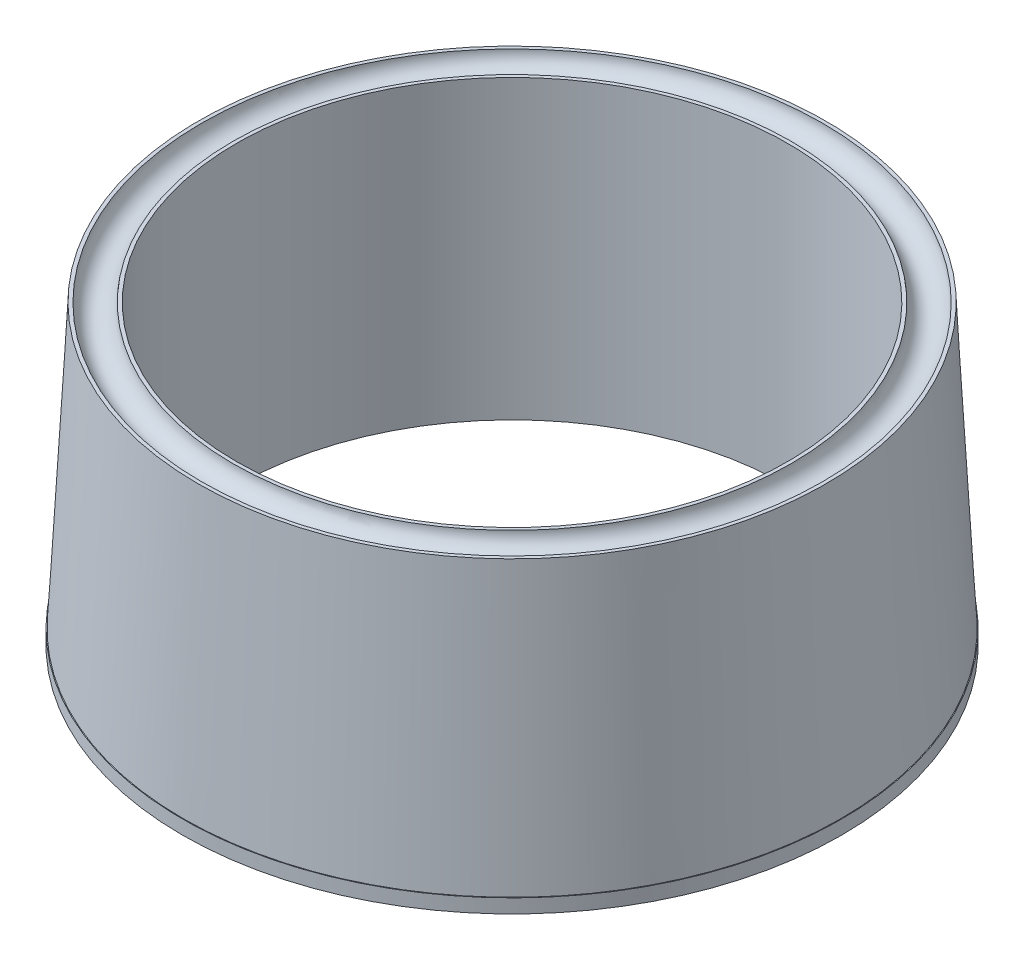
SolidWorks part; units mm, degrees
ref_plane "Płaszczyzna przednia" through (0, 0, 0) normal (0, 0, 1) x (1, 0, 0)
ref_plane "Płaszczyzna górna" through (0, 0, 0) normal (0, 1, 0) x (1, 0, 0)
ref_plane "Płaszczyzna prawa" through (0, 0, 0) normal (1, 0, 0) x (0, 0, -1)
sketch "Sketch1" plane through (0, 0, 0) normal (0, 1, 0) x (1, 0, 0)
  circle A0 centre (0, 0) radius 45
extrude "Boss-Extrude1" add sketch "Sketch1" along normal blind 42.5
sketch "Sketch2" plane through (0, 42.5, 0) normal (0, 1, 0) x (1, 0, 0)
  circle A0 centre (0, 0) radius 39.5
extrude "Cut-Extrude1" cut sketch "Sketch2" against normal blind 148
draft "Draft2" type of draft neutral plane draft angle 3 faces to draft 1 face at (0, 42.5, 45) neutral plane through (0, 42.5, 0) neutral plane normal (0, 1, 0) parameters "D1"=3
sketch "Sketch5" plane through (0, 0, 0) normal (0, -1, 0) x (1, 0, 0)
  line L0 (-39.5, 0) -> (-47.2273, 0)
  circle A0 centre (0, 0) radius 39.5 construction
  circle A1 centre (0, 0) radius 47.2273 construction
  dimension "D1" = 7.7273
sketch "Sketch6" plane through (0, 0, 0) normal (0, -1, 0) x (1, 0, 0)
  line L0 (-39.5, 0) -> (-47.2273, 0) construction
  line L1 (-43.3637, 0) -> (-21.6818, -37.554)
  line L2 (-21.6818, -37.554) -> (21.6818, -37.554)
  line L3 (21.6818, -37.554) -> (43.3637, 0)
  line L4 (43.3637, 0) -> (21.6818, 37.554)
  line L5 (21.6818, 37.554) -> (-21.6818, 37.554)
  line L6 (-21.6818, 37.554) -> (-43.3637, 0)
  line L7 (-21.6818, 34.2054) -> (-18.7818, 35.8797)
  line L8 (-18.7818, 35.8797) -> (-18.7818, 39.2284)
  line L9 (-18.7818, 39.2284) -> (-21.6818, 40.9027)
  line L10 (-21.6818, 40.9027) -> (-24.5818, 39.2284)
  line L11 (-24.5818, 39.2284) -> (-24.5818, 35.8797)
  line L12 (-24.5818, 35.8797) -> (-21.6818, 34.2054)
  line L13 (21.6818, 34.2054) -> (24.5818, 35.8797)
  line L14 (24.5818, 35.8797) -> (24.5818, 39.2284)
  line L15 (24.5818, 39.2284) -> (21.6818, 40.9027)
  line L16 (21.6818, 40.9027) -> (18.7818, 39.2284)
  line L17 (18.7818, 39.2284) -> (18.7818, 35.8797)
  line L18 (18.7818, 35.8797) -> (21.6818, 34.2054)
  line L19 (43.3637, -3.3486) -> (46.2637, -1.6743)
  line L20 (46.2637, -1.6743) -> (46.2637, 1.6743)
  line L21 (46.2637, 1.6743) -> (43.3637, 3.3486)
  line L22 (43.3637, 3.3486) -> (40.4637, 1.6743)
  line L23 (40.4637, 1.6743) -> (40.4637, -1.6743)
  line L24 (40.4637, -1.6743) -> (43.3637, -3.3486)
  line L25 (-43.3637, -3.3486) -> (-40.4637, -1.6743)
  line L26 (-40.4637, -1.6743) -> (-40.4637, 1.6743)
  line L27 (-40.4637, 1.6743) -> (-43.3637, 3.3486)
  line L28 (-43.3637, 3.3486) -> (-46.2637, 1.6743)
  line L29 (-46.2637, 1.6743) -> (-46.2637, -1.6743)
  line L30 (-46.2637, -1.6743) -> (-43.3637, -3.3486)
  line L31 (-21.6818, -34.2054) -> (-24.5818, -35.8797)
  line L32 (-24.5818, -35.8797) -> (-24.5818, -39.2284)
  line L33 (-24.5818, -39.2284) -> (-21.6818, -40.9027)
  line L34 (-21.6818, -40.9027) -> (-18.7818, -39.2284)
  line L35 (-18.7818, -39.2284) -> (-18.7818, -35.8797)
  line L36 (-18.7818, -35.8797) -> (-21.6818, -34.2054)
  line L37 (21.6818, -40.9027) -> (24.5818, -39.2284)
  line L38 (24.5818, -39.2284) -> (24.5818, -35.8797)
  line L39 (24.5818, -35.8797) -> (21.6818, -34.2054)
  line L40 (21.6818, -34.2054) -> (18.7818, -35.8797)
  line L41 (18.7818, -35.8797) -> (18.7818, -39.2284)
  line L42 (18.7818, -39.2284) -> (21.6818, -40.9027)
  circle A0 centre (0, 0) radius 37.554 construction
  circle A1 centre (-21.6818, 37.554) radius 2.9 construction
  circle A2 centre (21.6818, 37.554) radius 2.9 construction
  circle A3 centre (43.3637, 0) radius 2.9 construction
  circle A4 centre (-43.3637, 0) radius 2.9 construction
  circle A5 centre (-21.6818, -37.554) radius 2.9 construction
  circle A6 centre (21.6818, -37.554) radius 2.9 construction
  dimension "D1" = 2.9
  dimension "D2" = 0.9637
  dimension "D3" = 2.9
  dimension "D4" = 2.9
  dimension "D5" = 2.9
  dimension "D6" = 2.9
  dimension "D7" = 2.9
  dimension "D8" = 2.9
  dimension "D9" = 43.3637
extrude "Cut-Extrude2" cut sketch "Sketch6" against normal blind 5 contours L11 L12 L6 L5 L8 L9 L10 | L16 L17 L5 L4 L13 L14 L15 | L3 L24 L19 L20 L21 L22 L4 | L41 L42 L37 L38 L39 L3 L2 | L34 L35 L2 L1 L31 L32 L33 | L29 L30 L25 L1 L6 L27 L28 | L26 L27 L6 L1 L25 | L6 L12 L7 L8 L5 | L17 L18 L13 L4 L5 | L23 L24 L3 L4 L22 | L40 L41 L2 L3 L39 | L35 L36 L31 L1 L2
sketch "Sketch7" plane through (0, 0, 0) normal (0, -1, 0) x (1, 0, 0)
  circle A0 centre (0, 0) radius 47.2273
extrude "Boss-Extrude2" add sketch "Sketch7" against normal blind 2
sketch "Sketch8" plane through (0, 2, 0) normal (0, 1, 0) x (1, 0, 0)
  circle A0 centre (0, 0) radius 39.5
extrude "Cut-Extrude3" cut sketch "Sketch8" against normal blind 66
sketch "Sketch9" plane through (0, 0, 0) normal (0, -1, 0) x (1, 0, 0)
  line L1 (-43.36, 0) -> (-21.68, -37.5509)
  line L2 (-21.68, -37.5509) -> (21.68, -37.5509)
  line L3 (21.68, -37.5509) -> (43.36, 0)
  line L4 (43.36, 0) -> (21.68, 37.5509)
  line L5 (21.68, 37.5509) -> (-21.68, 37.5509)
  line L6 (-21.68, 37.5509) -> (-43.36, 0)
  circle A0 centre (0, 0) radius 37.5509 construction
  circle A1 centre (-43.36, 0) radius 1.7
  circle A2 centre (-21.68, 37.5509) radius 1.7
  circle A3 centre (21.68, 37.5509) radius 1.7
  circle A4 centre (43.36, 0) radius 1.7
  circle A5 centre (21.68, -37.5509) radius 1.7
  circle A6 centre (-21.68, -37.5509) radius 1.7
  dimension "D1" = 43.36
extrude "Cut-Extrude4" cut sketch "Sketch9" against normal blind 15 contours L6 A1 L1 | L1 A1 L6 | L5 A2 L6 | L5 A3 L4 | L4 A3 L5 | L4 A4 L3 | L3 A4 L4 | L2 A5 L3 | L3 A5 L2 | L1 A6 L2 | L2 A6 L1
sketch "Sketch10" plane through (0, 42.5, 0) normal (0, 1, 0) x (1, 0, 0)
  circle A2 centre (0, 0) radius 42.25
sweep "Cut-Sweep1" cut path "Sketch10" circular profile diameter 4.5 parameters "D3"=4.5
